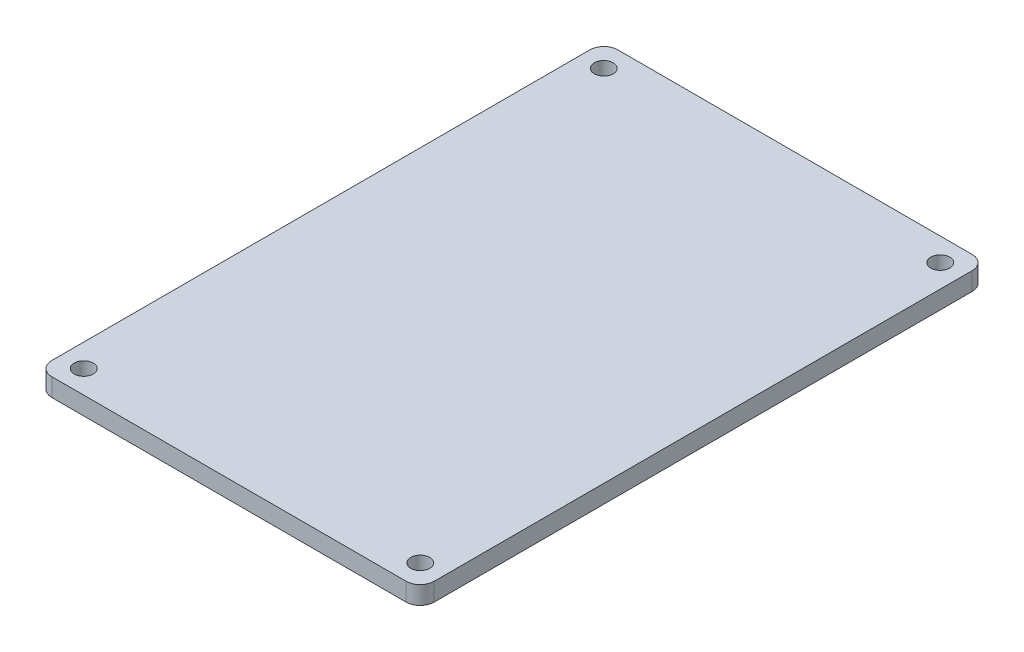
SolidWorks part; units mm, degrees
ref_plane "Front" through (0, 0, 0) normal (0, 0, 1) x (1, 0, 0)
ref_plane "Top" through (0, 0, 0) normal (0, 1, 0) x (1, 0, 0)
ref_plane "Right" through (0, 0, 0) normal (1, 0, 0) x (0, 0, -1)
sketch "Sketch1" plane through (0, 0, 0) normal (0, 1, 0) x (1, 0, 0)
  line L1 (-29.43, -47) -> (29.43, -47)
  line L2 (-31.75, -44.68) -> (-31.75, 44.68)
  line L3 (-29.43, 47) -> (29.43, 47)
  line L4 (31.75, -44.68) -> (31.75, 44.68)
  line L5 (-31.75, -47) -> (31.75, 47) construction
  line L6 (-31.75, 47) -> (31.75, -47) construction
  arc A0 (-29.43, -47) -> (-31.75, -44.68) centre (-29.43, -44.68) cw
  arc A1 (29.43, -47) -> (31.75, -44.68) centre (29.43, -44.68) ccw
  arc A2 (29.43, 47) -> (31.75, 44.68) centre (29.43, 44.68) cw
  arc A3 (-29.43, 47) -> (-31.75, 44.68) centre (-29.43, 44.68) ccw
  point P0 (0, 0)
  dimension "D3" = 2.32
  dimension "D1" = 94
  dimension "D2" = 63.5
extrude "Boss-Extrude1" add sketch "Sketch1" along normal blind 3
sketch "Sketch2" plane through (0, 3, 0) normal (0, 1, 0) x (1, 0, 0)
  point P0 (-27.94, 43.18)
  point P1 (27.94, 43.18)
  point P2 (27.94, -43.18)
  point P3 (-27.94, -43.18)
  dimension "D1" = 86.36
  dimension "D2" = 43.18
  dimension "D3" = 27.94
  dimension "D4" = 55.88
hole_wizard "Ø1.0mm Dowel Hole1" positions "Sketch4" profile "Sketch5" hole size "Ø1.0" standard "ANSI Metric" end condition through all
sketch "Sketch4" plane through (0, 3, 0) normal (0, 1, 0) x (1, 0, 0)
  point P0 (27.94, 43.18)
  point P3 (-27.94, 43.18)
  point P6 (-27.94, -43.18)
  point P9 (27.94, -43.18)
sketch "Sketch5" plane through (27.94, 3, -43.18) normal (1, 0, 0) x (0, 0, 1)
  line L0 (0, 0) -> (0, 3)
  line L1 (0, 3) -> (1.58, 3)
  line L2 (1.58, 3) -> (1.58, 0)
  line L5 (1.58, 0) -> (0, 0)
  line L11 (0, -6.35) -> (0, 107.95) construction
  dimension "Thru Hole Dia." = 3.16
  dimension "Thru Hole Depth" = 3
